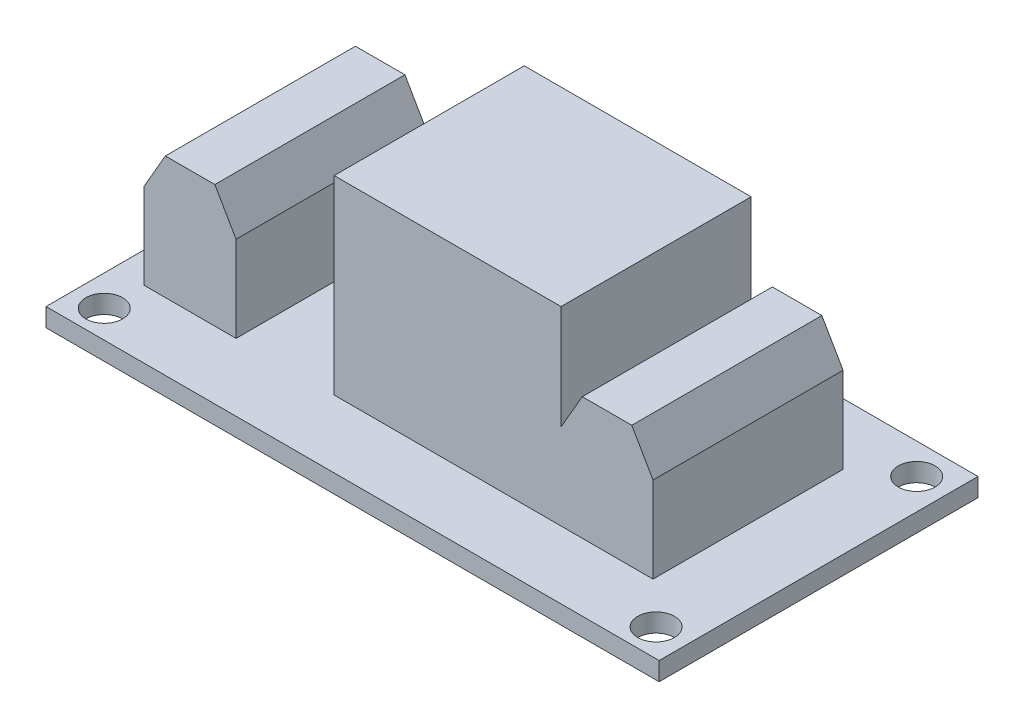
SolidWorks part; units mm, degrees
ref_plane "Alzado" through (0, 0, 0) normal (0, 0, 1) x (1, 0, 0)
ref_plane "Planta" through (0, 0, 0) normal (0, 1, 0) x (1, 0, 0)
ref_plane "Vista lateral" through (0, 0, 0) normal (1, 0, 0) x (0, 0, -1)
sketch "Croquis1" plane through (0, 0, 0) normal (0, 1, 0) x (1, 0, 0)
  line L1 (-25, -13) -> (25, -13)
  line L2 (-25, -13) -> (-25, 13)
  line L3 (-25, 13) -> (25, 13)
  line L4 (25, -13) -> (25, 13)
  line L5 (-25, -13) -> (25, 13) construction
  line L6 (-25, 13) -> (25, -13) construction
  point P0 (0, 0)
  dimension "D1" = 50
  dimension "D2" = 26
extrude "Saliente-Extruir1" add sketch "Croquis1" along normal blind 1.5
sketch "Croquis2" plane through (0, 1.5, 0) normal (0, 1, 0) x (1, 0, 0)
  line L0 (25, -13) -> (25, 13) construction
  line L1 (11.5, 8) -> (19, 8)
  line L2 (11.5, 8) -> (11.5, -7.5)
  line L3 (11.5, -7.5) -> (19, -7.5)
  line L4 (19, 8) -> (19, -7.5)
  line L5 (11.5, 8) -> (19, -7.5) construction
  line L6 (11.5, -7.5) -> (19, 8) construction
  line L7 (25, 13) -> (-25, 13) construction
  line L9 (-25, 13) -> (-25, -13) construction
  line L10 (-22.5, -7.5) -> (-15, -7.5)
  line L11 (-22.5, -7.5) -> (-22.5, 8)
  line L12 (-22.5, 8) -> (-15, 8)
  line L13 (-15, -7.5) -> (-15, 8)
  line L14 (-22.5, -7.5) -> (-15, 8) construction
  line L15 (-22.5, 8) -> (-15, -7.5) construction
  point P0 (15.25, 0.25)
  point P9 (-18.75, 0.25)
  dimension "D1" = 15.5
  dimension "D2" = 6
  dimension "D3" = 5
  dimension "D4" = 7.5
  dimension "D5" = 2.5
  dimension "D6" = 7.5
extrude "Saliente-Extruir2" add sketch "Croquis2" along normal blind 10
chamfer "Chaflán1" distance 3 angle 30 4 edges at (19, 11.5, -0.25) (11.5, 11.5, -0.25) (-15, 11.5, -0.25) (-22.5, 11.5, -0.25)
sketch "Croquis3" plane through (0, 1.5, 0) normal (0, 1, 0) x (1, 0, 0)
  line L0 (13.2321, -7.5) -> (17.2679, -7.5) construction
  line L1 (-7, -7.5) -> (11.5, -7.5)
  line L2 (-7, -7.5) -> (-7, 8)
  line L3 (-7, 8) -> (11.5, 8)
  line L4 (11.5, -7.5) -> (11.5, 8)
  line L5 (-7, -7.5) -> (11.5, 8) construction
  line L6 (-7, 8) -> (11.5, -7.5) construction
  point P0 (2.25, 0.25)
  dimension "D1" = 18.5
extrude "Saliente-Extruir3" add sketch "Croquis3" along normal blind 15.5
sketch "Croquis4" plane through (0, 0, 0) normal (0, -1, 0) x (1, 0, 0)
  line L1 (-15, -7.5) -> (15, -7.5)
  line L2 (-15, -7.5) -> (-15, 7.5)
  line L3 (-15, 7.5) -> (15, 7.5)
  line L4 (15, -7.5) -> (15, 7.5)
  line L5 (-15, -7.5) -> (15, 7.5) construction
  line L6 (-15, 7.5) -> (15, -7.5) construction
  point P0 (0, 0)
  dimension "D1" = 30
  dimension "D2" = 15
extrude "Saliente-Extruir4" add sketch "Croquis4" along normal blind 2
sketch "Croquis5" plane through (0, 0, 0) normal (0, -1, 0) x (1, 0, 0)
  line L0 (-25, -13) -> (-25, 13) construction
  line L1 (25, 13) -> (25, -13) construction
  line L2 (25, -13) -> (-25, -13) construction
  line L3 (-25, 13) -> (25, 13) construction
  circle A0 centre (-22.5, 10.75) radius 1.5
  circle A1 centre (22.5, 10.75) radius 1.5
  circle A2 centre (22.5, -10.5) radius 1.5
  circle A3 centre (-22.5, -10.5) radius 1.5
  point P8 (0, 0)
  point P9 (0, 0)
  point P10 (0, 0)
  point P11 (0, 0)
  dimension "D1" = 3
  dimension "D2" = 2.5
  dimension "D3" = 2.5
  dimension "D4" = 2.5
  dimension "D5" = 2.25
extrude "Cortar-Extruir1" cut sketch "Croquis5" against normal blind 2
